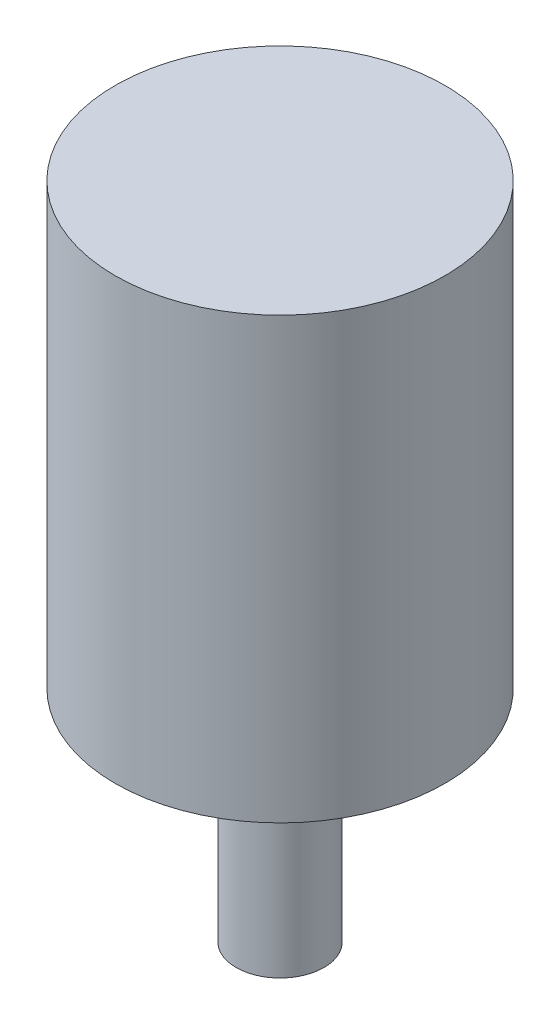
SolidWorks part; units mm, degrees
ref_plane "Front Plane" through (0, 0, 0) normal (0, 0, 1) x (1, 0, 0)
ref_plane "Top Plane" through (0, 0, 0) normal (0, 1, 0) x (1, 0, 0)
ref_plane "Right Plane" through (0, 0, 0) normal (1, 0, 0) x (0, 0, -1)
sketch "Croquis1" plane through (0, 0, 0) normal (0, 1, 0) x (1, 0, 0)
  circle A0 centre (0, 0) radius 0.375
  dimension "D1" = 0.75
extrude "Saliente-Extruir1" add sketch "Croquis1" along normal blind 1
sketch "Croquis2" plane through (0, 0, 0) normal (0, -1, 0) x (-1, 0, 0)
  circle A0 centre (0, 0) radius 0.1
  dimension "D1" = 0.2
extrude "Saliente-Extruir2" add sketch "Croquis2" along normal blind 0.5
